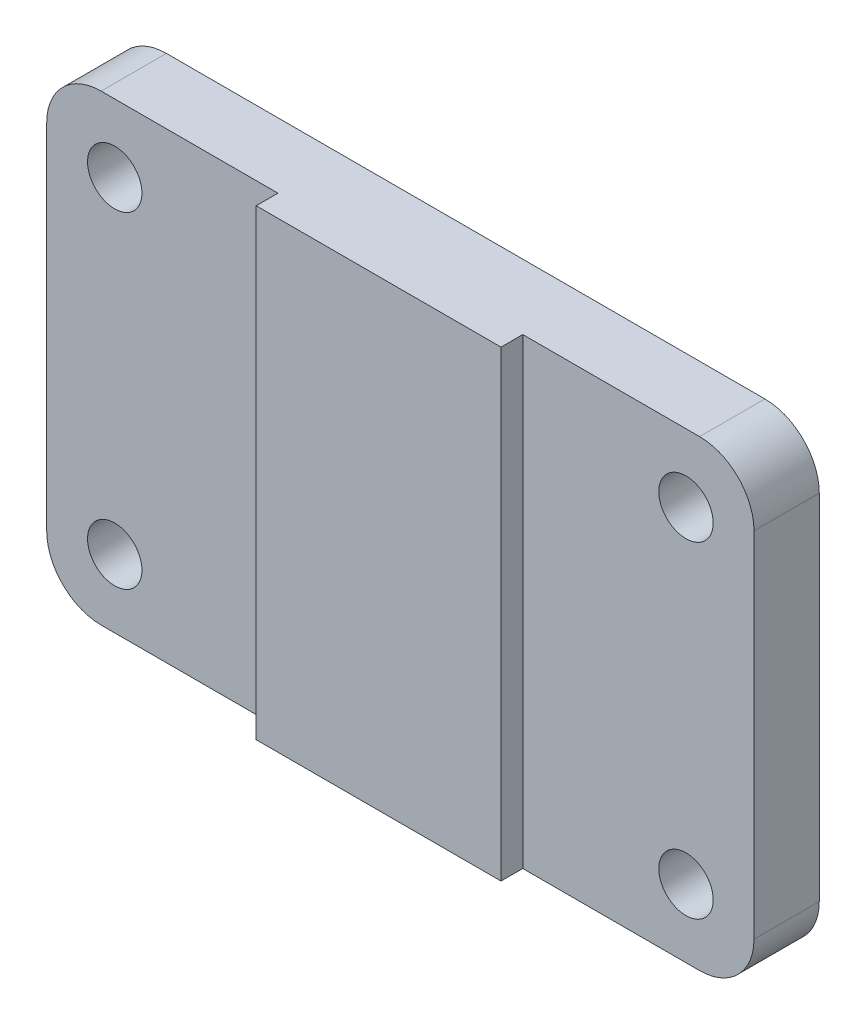
SolidWorks part; units mm, degrees
ref_plane "Front Plane" through (0, 0, 0) normal (0, 0, 1) x (1, 0, 0)
ref_plane "Top Plane" through (0, 0, 0) normal (0, 1, 0) x (1, 0, 0)
ref_plane "Right Plane" through (0, 0, 0) normal (1, 0, 0) x (0, 0, -1)
other "Configuration Table"
sketch "Sketch1" plane through (0, 0, 0) normal (0, 1, 0) x (1, 0, 0)
  line L0 (0, 0) -> (65, 0)
  line L1 (65, 0) -> (65, -12)
  line L2 (65, -12) -> (22.5, -12)
  line L3 (22.5, -12) -> (22.5, -16)
  line L4 (22.5, -16) -> (0, -16)
  line L5 (0, -16) -> (0, 0)
  dimension "D1" = 65
  dimension "D2" = 22.5
  dimension "D3" = 12
  dimension "D4" = 16
extrude "Extrude1" add sketch "Sketch1" along normal blind 85
hole_wizard "M10x1.25 Tapped Hole1" positions "Sketch3" profile "Sketch2" tap size "M10x1.25" standard "Ansi Metric" end condition through all
sketch "Sketch3" plane through (0, 0, 12) normal (0, 0, 1) x (1, 0, 0)
  line L0 (0, 42.5) -> (52.5, 42.5) construction
  line L2 (0, 85) -> (0, 0) construction
  point P0 (52.5, 12.5)
  point P10 (52.5, 72.5)
  dimension "D1" = 52.5
  dimension "D2" = 30
  dimension "D3" = 30
sketch "Sketch2" plane through (52.5, 12.5, 12) normal (1, 0, 0) x (0, -1, 0)
  line L0 (0, 0) -> (0, 12)
  line L1 (0, 12) -> (5, 12)
  line L2 (5, 12) -> (5, 0)
  line L5 (5, 0) -> (0, 0)
  line L11 (0, -6.35) -> (0, 107.95) construction
  dimension "Thread Major Dia." = 10
  dimension "Thru Tap Drill Depth" = 12
fillet "Fillet1" radius 10 2 edges at (65, 85, 6) (65, 0, 6)
mirror "Mirror1" about plane through (0, 0, 0) normal (1, 0, 0) of "Fillet1", "M10x1.25 Tapped Hole1", "Extrude1"
